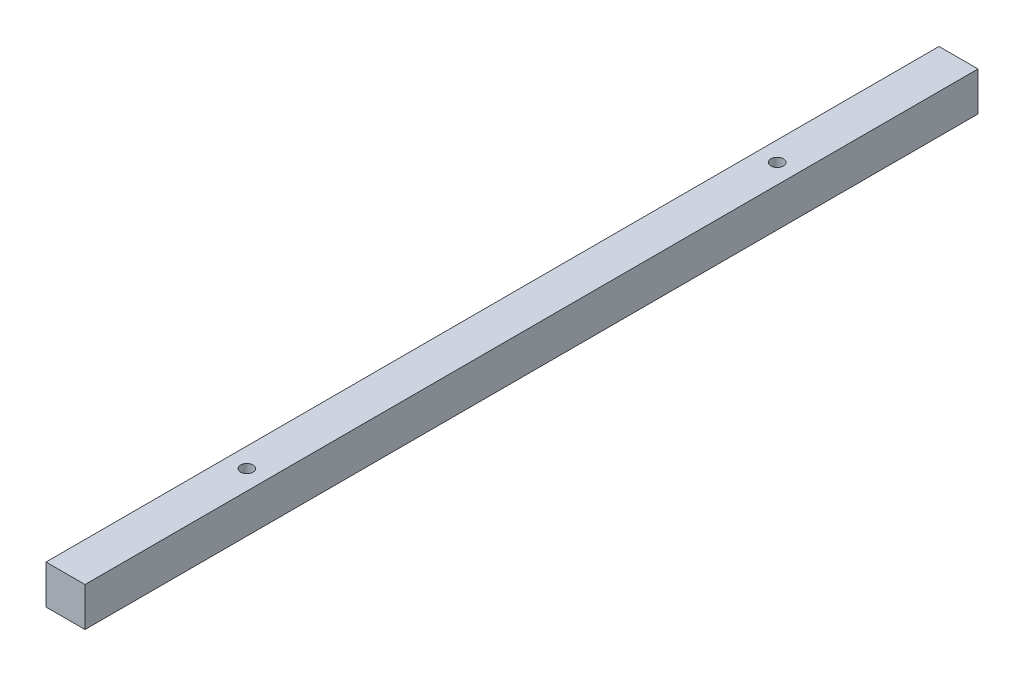
SolidWorks part; units mm, degrees
ref_plane "Plan de face" through (0, 0, 0) normal (0, 0, 1) x (1, 0, 0)
ref_plane "Plan de dessus" through (0, 0, 0) normal (0, 1, 0) x (1, 0, 0)
ref_plane "Plan de droite" through (0, 0, 0) normal (1, 0, 0) x (0, 0, -1)
sketch "Esquisse1" plane through (0, 0, 0) normal (0, 0, 1) x (1, 0, 0)
  line L0 (-5, 5) -> (5, -5) construction
  line L1 (-5, 5) -> (5, 5)
  line L2 (-5, 5) -> (-5, -5)
  line L3 (-5, -5) -> (5, -5)
  line L4 (5, 5) -> (5, -5)
  dimension "D1" = 10
extrude "Boss.-Extru.1" add sketch "Esquisse1" along normal up to surface (114.5 mm away) and the other way up to surface (114.5 mm away)
sketch "Esquisse2" plane through (0, 5, 0) normal (0, 1, 0) x (1, 0, 0)
  circle A0 centre (0, 68) radius 1.6
  circle A1 centre (0, -68) radius 1.6
  circle A2 centre (0, 68) radius 1.525 construction
  circle A3 centre (0, -68) radius 1.525 construction
  dimension "D1" = 3.2
extrude "Enlèv. mat.-Extru.1" cut sketch "Esquisse2" against normal through all
